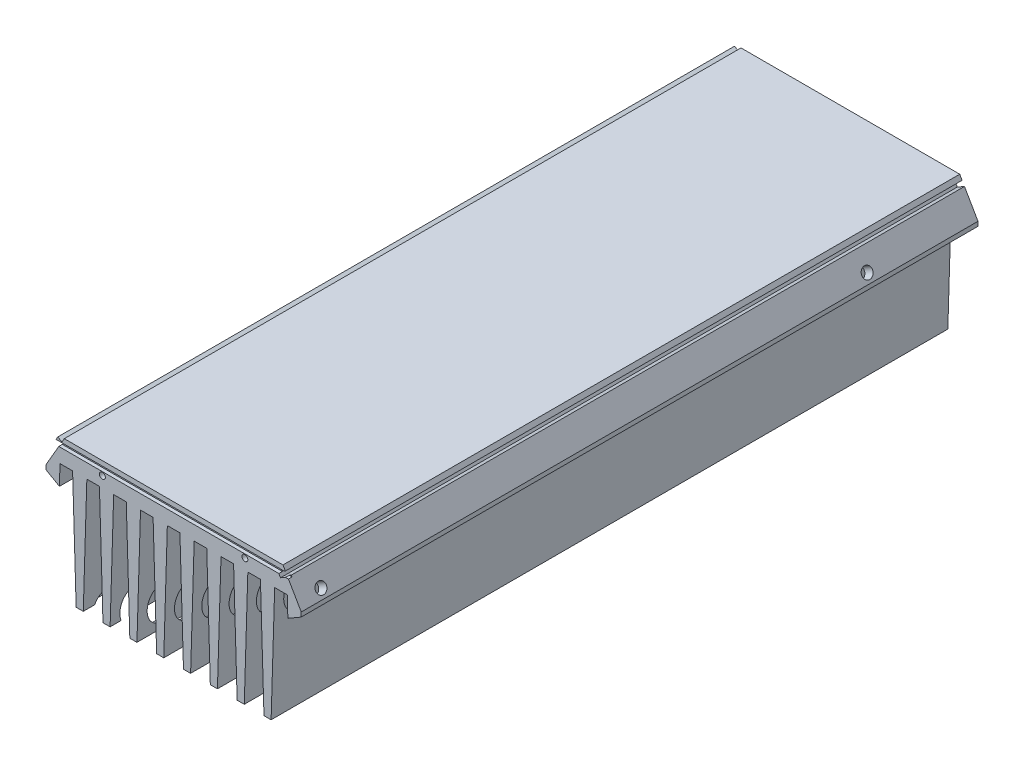
SolidWorks part; units mm, degrees
ref_plane "Plano frontal" through (0, 0, 0) normal (0, 0, 1) x (1, 0, 0)
ref_plane "Plano superior" through (0, 0, 0) normal (0, 1, 0) x (1, 0, 0)
ref_plane "Plano direito" through (0, 0, 0) normal (1, 0, 0) x (0, 0, -1)
sketch "Esboço1" plane through (0, 0, 0) normal (0, 0, 1) x (1, 0, 0)
  line L0 (0, 59) -> (155, 59)
  line L3 (0, 0) -> (131.9536, 0) construction
  line L4 (0, 49) -> (0, 59)
  line L46 (29.65, 49) -> (34.95, 49)
  line L47 (34.95, 49) -> (40.95, 49) construction
  line L48 (40.95, 49) -> (46.25, 49)
  line L49 (46.25, 49) -> (52.25, 49) construction
  line L50 (52.25, 49) -> (57.55, 49)
  line L51 (57.55, 49) -> (63.55, 49) construction
  line L52 (63.55, 49) -> (68.85, 49)
  line L53 (68.85, 49) -> (74.85, 49) construction
  line L54 (74.85, 49) -> (80.15, 49)
  line L57 (0, 0) -> (0, 59) construction
  line L59 (0, 49) -> (1.05, 49)
  line L61 (1.05, 49) -> (7.05, 49) construction
  line L63 (7.05, 49) -> (12.35, 49)
  line L65 (12.35, 49) -> (18.35, 49) construction
  line L66 (29.65, 49) -> (28.15, 0)
  line L68 (34.95, 49) -> (36.45, 0)
  line L69 (36.45, 0) -> (39.45, 0)
  line L70 (39.45, 0) -> (40.95, 49)
  line L71 (46.25, 49) -> (47.75, 0)
  line L72 (47.75, 0) -> (50.75, 0)
  line L73 (50.75, 0) -> (52.25, 49)
  line L74 (57.55, 49) -> (59.05, 0)
  line L75 (59.05, 0) -> (62.05, 0)
  line L76 (62.05, 0) -> (63.55, 49)
  line L77 (68.85, 49) -> (70.35, 0)
  line L78 (70.35, 0) -> (73.35, 0)
  line L79 (73.35, 0) -> (74.85, 49)
  line L97 (77.5, 49) -> (77.5, 59) construction
  line L98 (37.95, 0) -> (37.95, 49) construction
  line L99 (18.35, 49) -> (23.65, 49)
  line L100 (23.65, 49) -> (29.65, 49) construction
  line L101 (131.35, 49) -> (125.35, 49) construction
  line L102 (117.05, 0) -> (117.05, 49) construction
  line L103 (142.65, 49) -> (136.65, 49) construction
  line L104 (153.95, 49) -> (147.95, 49) construction
  line L105 (1.05, 49) -> (2.55, 0)
  line L106 (2.55, 0) -> (5.55, 0)
  line L107 (5.55, 0) -> (7.05, 49)
  line L108 (12.35, 49) -> (13.85, 0)
  line L109 (13.85, 0) -> (16.85, 0)
  line L110 (16.85, 0) -> (18.35, 49)
  line L111 (23.65, 49) -> (25.15, 0)
  line L112 (25.15, 0) -> (28.15, 0)
  line L113 (86.15, 49) -> (80.15, 49) construction
  line L114 (97.45, 49) -> (91.45, 49) construction
  line L115 (108.75, 49) -> (102.75, 49) construction
  line L116 (120.05, 49) -> (114.05, 49) construction
  line L117 (129.85, 0) -> (126.85, 0)
  line L118 (131.35, 49) -> (129.85, 0)
  line L119 (138.15, 0) -> (136.65, 49)
  line L120 (141.15, 0) -> (138.15, 0)
  line L121 (142.65, 49) -> (141.15, 0)
  line L122 (149.45, 0) -> (147.95, 49)
  line L123 (152.45, 0) -> (149.45, 0)
  line L124 (153.95, 49) -> (152.45, 0)
  line L125 (136.65, 49) -> (131.35, 49)
  line L126 (81.65, 0) -> (80.15, 49)
  line L127 (84.65, 0) -> (81.65, 0)
  line L128 (86.15, 49) -> (84.65, 0)
  line L129 (92.95, 0) -> (91.45, 49)
  line L130 (95.95, 0) -> (92.95, 0)
  line L131 (97.45, 49) -> (95.95, 0)
  line L132 (104.25, 0) -> (102.75, 49)
  line L133 (107.25, 0) -> (104.25, 0)
  line L134 (108.75, 49) -> (107.25, 0)
  line L135 (115.55, 0) -> (114.05, 49)
  line L136 (118.55, 0) -> (115.55, 0)
  line L137 (120.05, 49) -> (118.55, 0)
  line L138 (125.35, 49) -> (126.85, 0)
  line L139 (147.95, 49) -> (142.65, 49)
  line L140 (155, 49) -> (153.95, 49)
  line L141 (91.45, 49) -> (86.15, 49)
  line L142 (102.75, 49) -> (97.45, 49)
  line L143 (114.05, 49) -> (108.75, 49)
  line L144 (125.35, 49) -> (120.05, 49)
  line L145 (155, 49) -> (155, 59)
  point P0 (6.6703, 49)
  point P2 (77.5, 49)
  dimension "D1" = 155
  dimension "D2" = 59
  dimension "D3" = 5.3
  dimension "D4" = 10
  dimension "D5" = 11.3
  dimension "D6" = 3
extrude "Ressalto-extrusão1" add sketch "Esboço1" along normal blind 285
sketch "Esboço2" plane through (0, 0, 0) normal (0, 0, -1) x (-1, 0, 0)
  line L1 (-155, 59) -> (0, 59) construction
  line L2 (-124.5538, 57.2679) -> (-123.5538, 59) construction
  line L3 (-125.5538, 55.5359) -> (-132.0538, 44.2776)
  line L4 (-132.0538, 44.2776) -> (-123.3936, 39.2776)
  line L5 (-123.3936, 39.2776) -> (-123.3936, -2.1816)
  line L6 (-123.3936, -2.1816) -> (-157.2094, -2.1816)
  line L7 (-157.2094, -2.1816) -> (-157.2094, 65.2148)
  line L8 (-157.2094, 65.2148) -> (-123.5538, 65.2148)
  line L9 (-123.5538, 65.2148) -> (-123.5538, 59)
  line L10 (-31.4462, 59) -> (7.5297, 59)
  line L11 (-31.4462, 59) -> (-30.4462, 57.2679) construction
  line L12 (7.5297, 59) -> (7.5297, -3.4441)
  line L13 (7.5297, -3.4441) -> (-31.6064, -3.4441)
  line L14 (-31.6064, -3.4441) -> (-31.6064, 39.2776)
  line L15 (-34.1064, 43.6077) -> (-31.6064, 39.2776) construction
  line L16 (-31.6064, 39.2776) -> (-22.9462, 44.2776)
  line L17 (-22.9462, 44.2776) -> (-29.4462, 55.5359)
  line L18 (-29.4462, 55.5359) -> (-27.7141, 56.5359)
  line L19 (-27.7141, 56.5359) -> (-28.7141, 58.2679)
  line L20 (-28.7141, 58.2679) -> (-30.4462, 57.2679)
  line L21 (-30.4462, 57.2679) -> (-31.4462, 59)
  line L22 (-128.75, 50) -> (-125.5538, 55.5359) construction
  line L23 (-125.5538, 55.5359) -> (-122.5228, 53.7859)
  line L24 (-122.5228, 53.7859) -> (-121.5228, 55.5179)
  line L25 (-121.5228, 55.5179) -> (-124.5538, 57.2679)
  line L26 (-124.5538, 57.2679) -> (-121.5228, 55.5179) construction
  line L27 (-124.5538, 57.2679) -> (-123.5538, 59)
extrude "Corte-extrusão1" cut sketch "Esboço2" against normal through all both and the other way through all
sketch "Esboço3" plane through (0, 0, 285) normal (0, 0, 1) x (1, 0, 0)
  circle A0 centre (47.5, 53.5) radius 1.25
  circle A1 centre (107.5, 53.5) radius 1.25
  dimension "D1" = 2.5
  dimension "D2" = 2.5
extrude "Corte-extrusão2" cut sketch "Esboço3" against normal blind 10
sketch "Esboço4" plane through (9.615, -2.5557, 0) normal (1, 0, 0) x (0, 0, -1)
  line L0 (-285, 57.5557) -> (-283.5, 57.5557)
  line L1 (-283.5, 57.5557) -> (-283.5, 59.5557)
  line L2 (-283.5, 59.5557) -> (-285, 59.5557)
  line L3 (-285, 59.5557) -> (-285, 57.5557)
  line L4 (-285, 60.8237) -> (-285, 59.0916) construction
  point P2 (-283.5, 57.5557)
  point P5 (-285, 59.4348)
  point P9 (-283.5, 59.5846)
  point P10 (-283.5, 59.5557)
extrude "Corte-extrusão3" cut sketch "Esboço4" against normal through all both and the other way through all
sketch "Esboço5" plane through (-1.9631, 1.1334, 0) normal (-0.866, 0.5, 0) x (0, 0, 1)
  circle A0 centre (45, 54.8186) radius 1.65
  circle A1 centre (275, 54.8186) radius 1.65
  dimension "D1" = 3.3
extrude "Corte-extrusão4" cut sketch "Esboço5" against normal blind 10
sketch "Esboço6" plane through (118.2131, 68.2504, 0) normal (0.866, 0.5, 0) x (0, 0, -1)
  circle A0 centre (-275, -22.6814) radius 2.25
  circle A1 centre (-45, -22.6814) radius 2.25
  dimension "D1" = 4.5
extrude "Corte-extrusão5" cut sketch "Esboço6" against normal through all both and the other way through all
sketch "Esboço8" plane through (118.2131, 68.2504, 0) normal (0.866, 0.5, 0) x (0, 0, -1)
  circle A0 centre (-275, -22.6814) radius 6
  circle A1 centre (-45, -22.6814) radius 6
  dimension "D1" = 12
extrude "Corte-extrusão6" cut sketch "Esboço8" against normal blind 100 from offset 4
